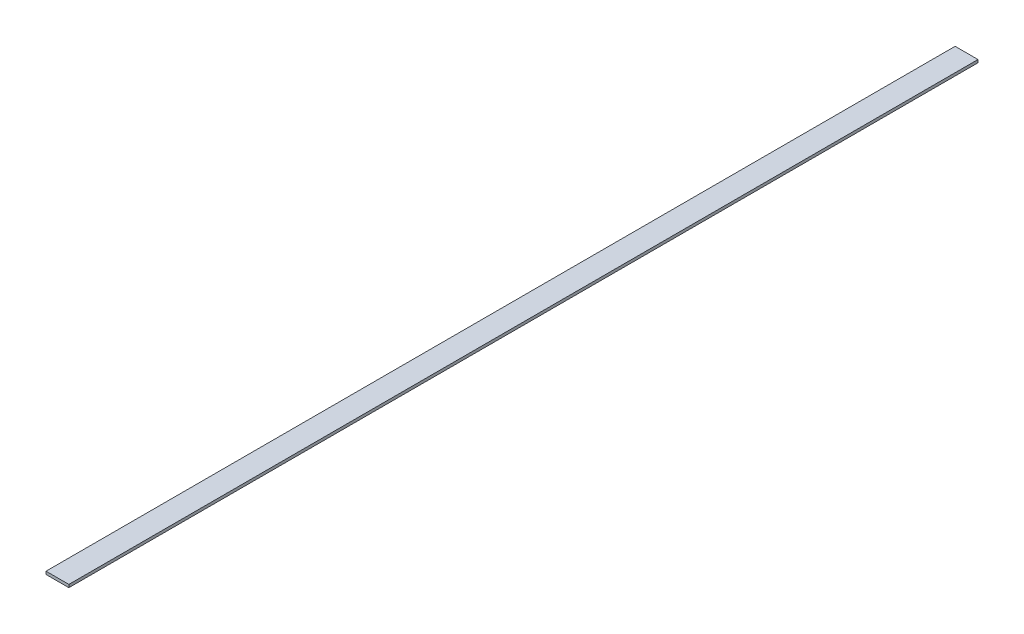
SolidWorks part; units mm, degrees
material "ABS"
ref_plane "Front Plane" through (0, 0, 0) normal (0, 0, 1) x (1, 0, 0)
ref_plane "Top Plane" through (0, 0, 0) normal (0, 1, 0) x (1, 0, 0)
ref_plane "Right Plane" through (0, 0, 0) normal (1, 0, 0) x (0, 0, -1)
sketch "Sketch1" plane through (0, 0, 0) normal (0, 1, 0) x (1, 0, 0)
  line L1 (0, 0) -> (12.7, 0)
  line L2 (0, 0) -> (0, 505)
  line L3 (0, 505) -> (12.7, 505)
  line L4 (12.7, 0) -> (12.7, 505)
  dimension "D1" = 12.7
  dimension "D2" = 505
extrude "Boss-Extrude1" add sketch "Sketch1" along normal blind 1.59
equation "\"ABS_thickness\" = 1.59\t"
equation "\"Bus_bar_thickness\" = 3.175"
equation "\"Connector_width\" = 20.2"
equation "\"Number_of_cells_long\" = 25"
equation "\"Number_of_cells_wide\" = 2"
equation "\"Cell_height\" = 65.0"
equation "\"Cell_diam\" = 18.0"
equation "\"D2@Sketch1\"=\"Number_of_cells_long\"*\"Connector_width\""
equation "\"D1@Boss-Extrude1\"=\"ABS_thickness\""
